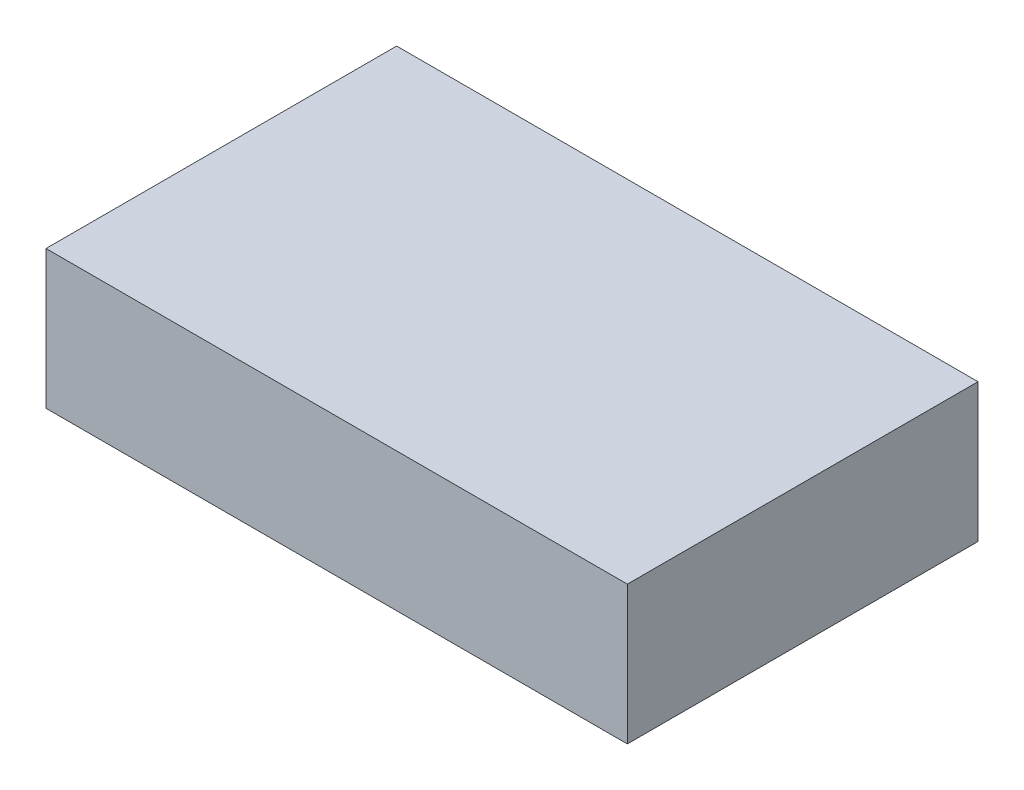
SolidWorks part; units mm, degrees
material "Plain Carbon Steel"
ref_plane "Front Plane" through (0, 0, 0) normal (0, 0, 1) x (1, 0, 0)
ref_plane "Top Plane" through (0, 0, 0) normal (0, 1, 0) x (1, 0, 0)
ref_plane "Right Plane" through (0, 0, 0) normal (1, 0, 0) x (0, 0, -1)
sketch "Sketch1" plane through (0, 0, 0) normal (0, 1, 0) x (1, 0, 0)
  line L0 (-80.01, 48.26) -> (80.01, -48.26) construction
  line L1 (80.01, 48.26) -> (-80.01, 48.26)
  line L2 (80.01, 48.26) -> (80.01, -48.26)
  line L3 (80.01, -48.26) -> (-80.01, -48.26)
  line L4 (-80.01, 48.26) -> (-80.01, -48.26)
  dimension "D1" = 160.02
  dimension "D2" = 96.52
extrude "Boss-Extrude1" add sketch "Sketch1" along normal blind 38.1
